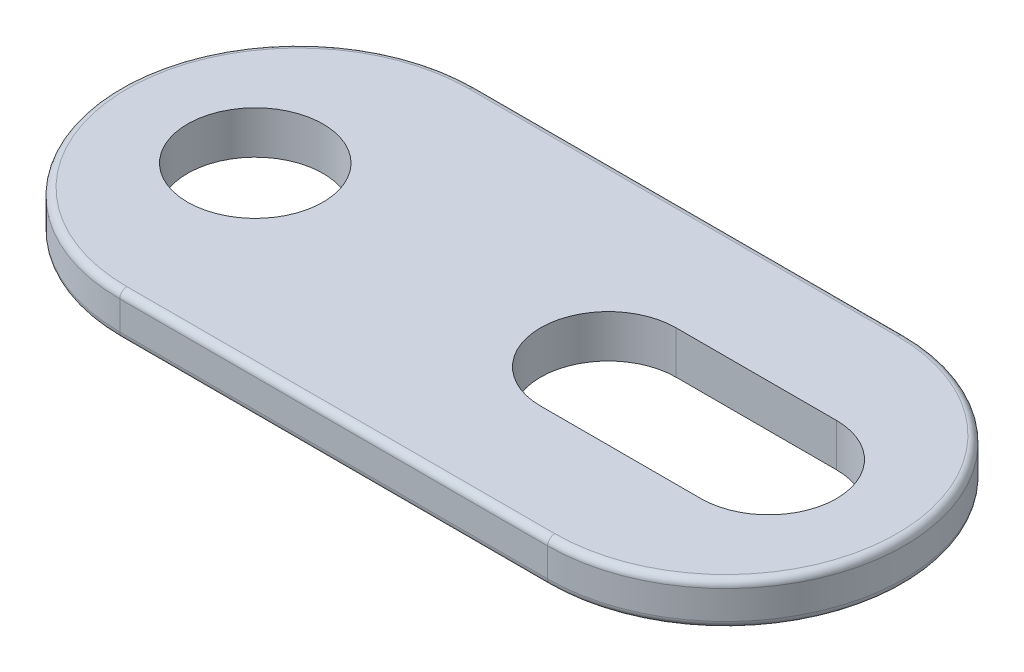
SolidWorks part; units mm, degrees
material "AISI 304"
ref_plane "Front" through (0, 0, 0) normal (0, 0, 1) x (1, 0, 0)
ref_plane "Top" through (0, 0, 0) normal (0, 1, 0) x (1, 0, 0)
ref_plane "Right" through (0, 0, 0) normal (1, 0, 0) x (0, 0, -1)
sketch "Sketch1" plane through (0, 0, 0) normal (0, 1, 0) x (1, 0, 0)
  line L1 (1.524, -6.35) -> (16.764, -6.35)
  line L2 (12.573, 2.413) -> (18.288, 2.413)
  line L3 (1.524, 6.35) -> (16.764, 6.35)
  line L5 (12.573, -2.413) -> (18.288, -2.413)
  arc A0 (1.524, 6.35) -> (1.524, -6.35) centre (1.524, 0) ccw
  arc A1 (16.764, -6.35) -> (16.764, 6.35) centre (16.764, 0) ccw
  circle A2 centre (0, 0) radius 2.413
  arc A3 (12.573, 2.413) -> (12.573, -2.413) centre (12.573, 0) ccw
  arc A4 (18.288, -2.413) -> (18.288, 2.413) centre (18.288, 0) ccw
  dimension "D3" = 4.826
  dimension "D1" = 12.7
  dimension "D2" = 15.24
  dimension "D4" = 1.524
  dimension "D5" = 4.826
  dimension "D6" = 2.413
  dimension "D7" = 1.524
  dimension "D8" = 5.715
sheet metal parameters "Sheet-Metal1" thickness 1.524 parameters "D1"=3.81
extrude "Extrude1" add sketch "Sketch1" along normal mid plane 1.524
fillet "Fillet1" radius 0.254 8 edges at (-4.826, 0.762, 0) (9.144, 0.762, -6.35) (23.114, 0.762, 0) (9.144, 0.762, 6.35) (-4.826, -0.762, 0) (9.144, -0.762, -6.35) (23.114, -0.762, 0) (9.144, -0.762, 6.35)
